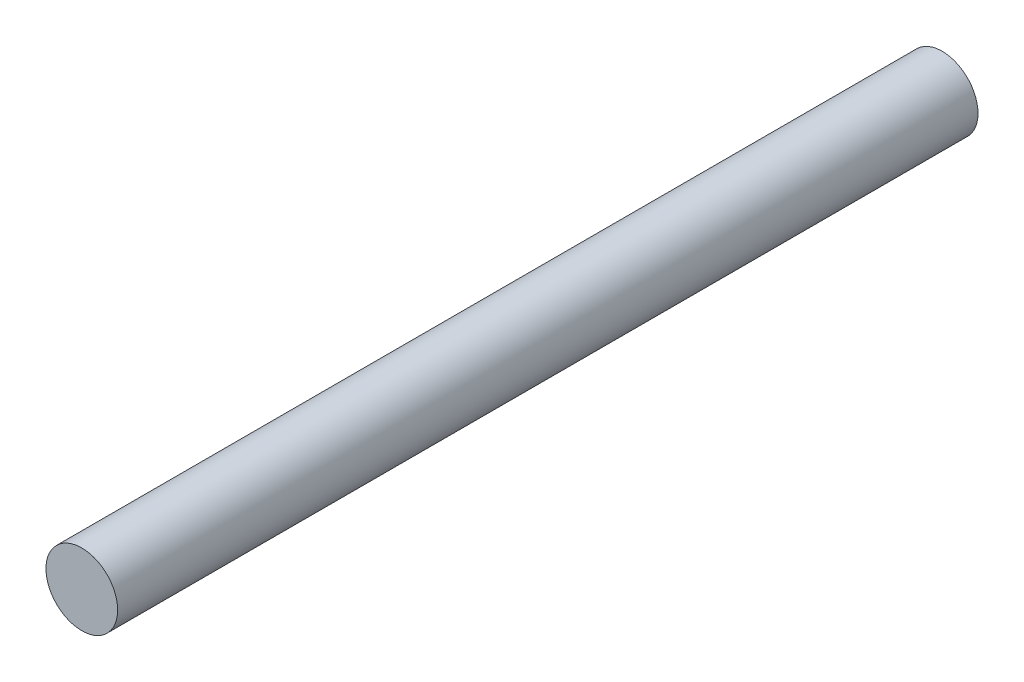
SolidWorks part; units mm, degrees
ref_plane "Front Plane" through (0, 0, 0) normal (0, 0, 1) x (1, 0, 0)
ref_plane "Top Plane" through (0, 0, 0) normal (0, 1, 0) x (1, 0, 0)
ref_plane "Right Plane" through (0, 0, 0) normal (1, 0, 0) x (0, 0, -1)
sketch "Sketch1" plane through (0, 0, 0) normal (0, 0, 1) x (1, 0, 0)
  circle A0 centre (0, 0) radius 2.5
  dimension "D1" = 5
extrude "Boss-Extrude1" add sketch "Sketch1" along normal blind 60
